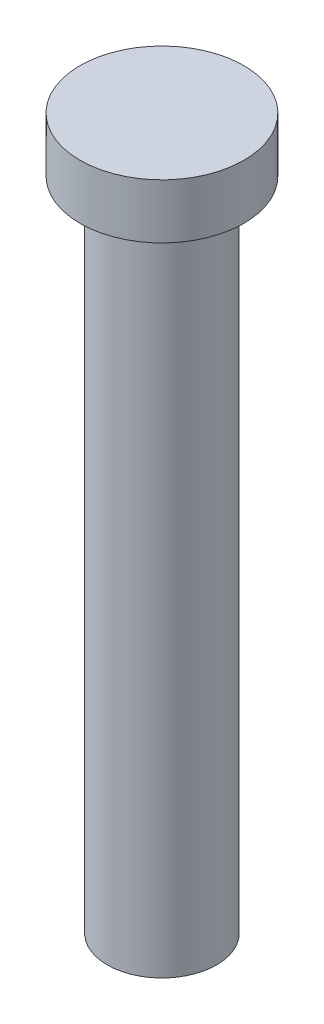
SolidWorks part; units mm, degrees
ref_plane "Front Plane" through (0, 0, 0) normal (0, 0, 1) x (1, 0, 0)
ref_plane "Top Plane" through (0, 0, 0) normal (0, 1, 0) x (1, 0, 0)
ref_plane "Right Plane" through (0, 0, 0) normal (1, 0, 0) x (0, 0, -1)
sketch "Sketch1" plane through (0, 0, 0) normal (0, 1, 0) x (1, 0, 0)
  circle A0 centre (0, 0) radius 6.35
  dimension "D1" = 12.7
extrude "Boss-Extrude1" add sketch "Sketch1" along normal blind 76.2
sketch "Sketch2" plane through (0, 76.2, 0) normal (0, 1, 0) x (1, 0, 0)
  circle A0 centre (0, 0) radius 9.525
  dimension "D1" = 19.05
extrude "Boss-Extrude2" add sketch "Sketch2" along normal blind 6.35
